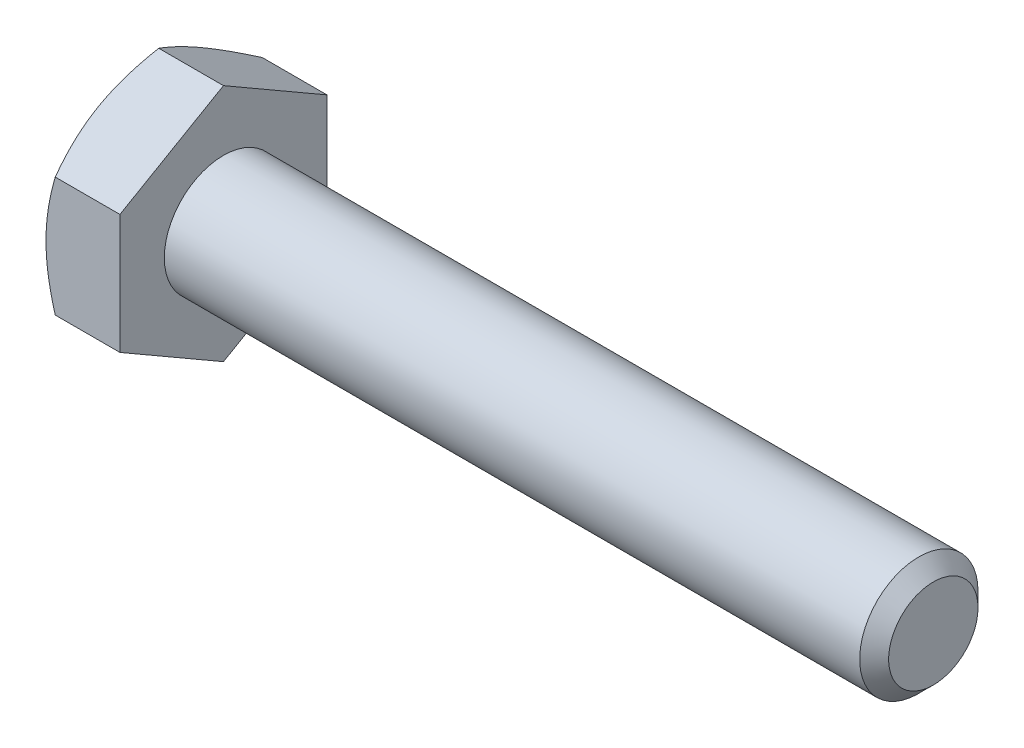
SolidWorks part; units mm, degrees
material "Alloy Steel"
ref_plane "Front Plane" through (0, 0, 0) normal (0, 0, 1) x (1, 0, 0)
ref_plane "Top Plane" through (0, 0, 0) normal (0, 1, 0) x (1, 0, 0)
ref_plane "Right Plane" through (0, 0, 0) normal (1, 0, 0) x (0, 0, -1)
sketch "Sketch1" plane through (0, 0, 0) normal (0, 0, 1) x (1, 0, 0)
  line L0 (-21.0344, 0) -> (21.0344, 0) construction
  line L1 (21.0344, 3.175) -> (21.0344, -3.175) construction
  line L2 (-17.0656, 5.5562) -> (-17.0656, -5.5562) construction
  line L3 (-21.0344, 5.5562) -> (-21.0344, -5.5562) construction
  point P9 (-17.0656, 0)
  point P10 (16.5894, -3.175)
  dimension "D1" = 4.445
  dimension "Screw Dia" = 6.35
  dimension "Hex" = 11.1125
  dimension "Head Ht" = 3.9688
  dimension "Screw Lenght" = 38.1
ref_plane "Plane2" through (21.0344, 0, 0) normal (1, 0, 0) x (0, 0, -1)
sketch "Sketch5" plane through (21.0344, 0, 0) normal (1, 0, 0) x (0, 0, -1)
  circle A0 centre (0, 0) radius 3.175
extrude "Boss-Extrude3" add sketch "Sketch5" against normal up to vertex (38.1 mm away) up to point (-17.0656, 0, 0)
sketch "Sketch9" plane through (21.0344, 0, 0) normal (1, 0, 0) x (0, 0, -1)
  circle A1 centre (0, 0) radius 3.175
  circle A2 centre (0, 0) radius 3.175
  dimension "D1" = 0
curve "Helix/Spiral1" pitch 1.27 height 39.37 turns 31 parameters "Pitch"=1.27
chamfer "Chamfer1" distance 0.7772 angle 45 1 edges at (21.0344, 0, -3.175)
sketch "Sketch10" plane through (0, 0, 0) normal (0, 0, 1) x (1, 0, 0)
  line L0 (21.0344, 3.175) -> (21.5106, 2.3501)
  line L1 (21.5106, 2.3501) -> (21.6694, 2.3501)
  line L2 (21.6694, 2.3501) -> (22.1456, 3.175)
  line L3 (21.0344, 3.175) -> (22.1456, 3.175)
  line L4 (21.59, 3.175) -> (21.59, 2.3501) construction
  line L5 (21.2725, 2.7626) -> (21.9075, 2.7626) construction
  dimension "D1" = 60
  dimension "D2" = 0.1588
  dimension "D3" = 0.635
sketch "Sketch6" plane through (-17.0656, 0, 0) normal (-1, 0, 0) x (0, 0, 1)
  line L0 (0, 5.5562) -> (0, -5.5562) construction
  line L1 (5.5563, 3.2079) -> (0, 6.4158)
  line L2 (0, 6.4158) -> (-5.5562, 3.2079)
  line L3 (-5.5562, 3.2079) -> (-5.5562, -3.2079)
  line L4 (-5.5562, -3.2079) -> (0, -6.4158)
  line L5 (0, -6.4158) -> (5.5563, -3.2079)
  line L6 (5.5563, -3.2079) -> (5.5563, 3.2079)
  circle A0 centre (0, 0) radius 5.5563 construction
extrude "Boss-Extrude4" add sketch "Sketch6" along normal up to vertex (3.9688 mm away) up to point (-21.0344, -5.5562, 0)
sketch "Sketch7" plane through (-21.0344, 0, 0) normal (-1, 0, 0) x (0, 0, 1)
  circle A0 centre (0, 0) radius 5.5563 construction
  circle A1 centre (0, 0) radius 5.5563
sketch "Sketch8" plane through (-21.0344, 0, 0) normal (-1, 0, 0) x (0, 0, 1)
  circle A0 centre (0, 0) radius 5.5563 construction
  circle A1 centre (0, 0) radius 5.5563
extrude "Cut-Extrude3" cut sketch "Sketch8" against normal through all draft 60 flip side to cut
sketch "Sketch12" plane through (-21.0344, 0, 0) normal (-1, 0, 0) x (0, 0, 1)
  line L0 (0, 4.2783) -> (0, 2.3892) construction
  line L1 (0.1667, 4.2783) -> (0.1667, 2.3892)
  line L2 (-0.1667, 4.2783) -> (-0.1667, 2.3892)
  line L3 (0, 3.175) -> (0, -3.175) construction
  arc A0 (0.1667, 4.2783) -> (-0.1667, 4.2783) centre (0, 4.2783) ccw
  arc A1 (-0.1667, 2.3892) -> (0.1667, 2.3892) centre (0, 2.3892) ccw
  circle A3 centre (0, 0) radius 2.2225 construction
  circle A4 centre (0, 0) radius 4.445 construction
  point P2 (0, 3.3337)
  dimension "D1" = 4.445
  dimension "D3" = 8.89
  dimension "D2" = 0.3334
extrude "Cut-Extrude4" cut sketch "Sketch12" against normal blind 0.254
pattern_circular "CirPattern1" count 3 over 360 about axis through (0, 0, 0) along (1, 0, 0) of "Cut-Extrude4"
equation "\"D2@Sketch10\" = \"Pitch@Helix/Spiral1\"*.125"
equation "\"D3@Sketch10\" = \"Pitch@Helix/Spiral1\"*.5"
equation "\"D1@Chamfer1\" = \"Pitch@Helix/Spiral1\"*.612"
equation "\"D1@Sketch12\" = \"Hex@Sketch1\"*.4"
equation "\"D3@Sketch12\" = \"Hex@Sketch1\"*.8"
equation "\"D2@Sketch12\" = \"Hex@Sketch1\"*.03"
equation "\"D1@Sketch1\" = \"Pitch@Helix/Spiral1\"*3.5"
equation "\"D3@Helix/Spiral1\" = \"Screw Lenght@Sketch1\"+\"Pitch@Helix/Spiral1\""
